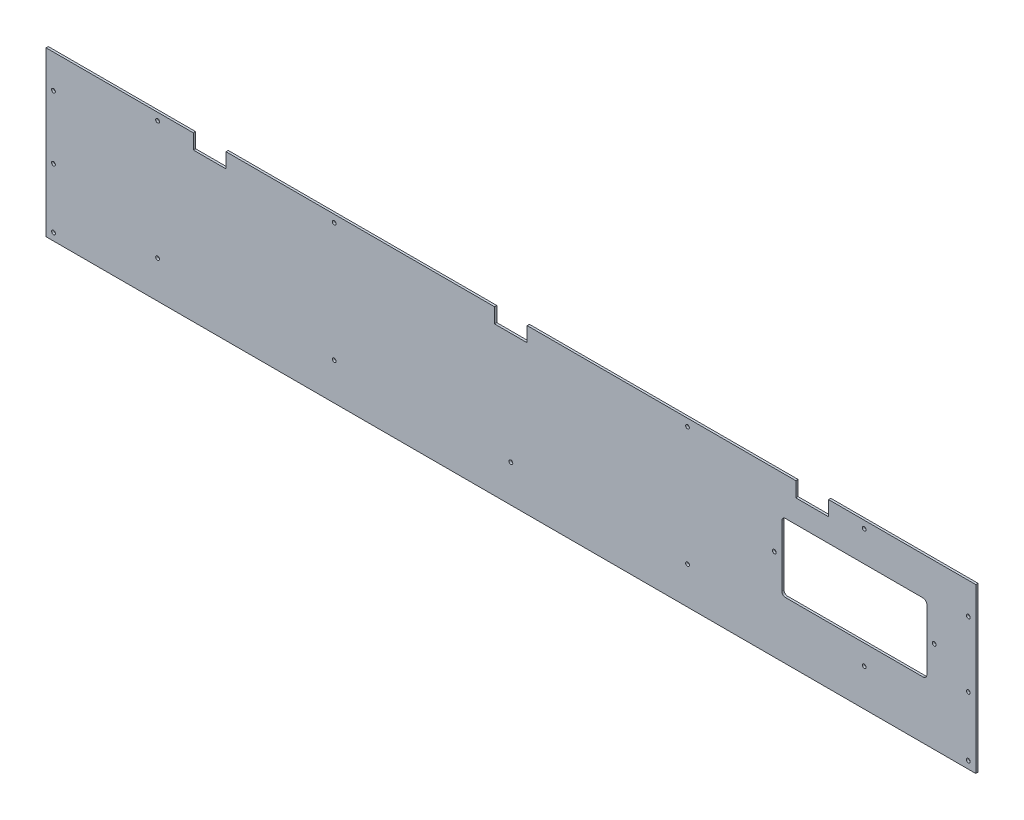
SolidWorks part; units mm, degrees
ref_plane "Front Plane" through (0, 0, 0) normal (0, 0, 1) x (1, 0, 0)
ref_plane "Top Plane" through (0, 0, 0) normal (0, 1, 0) x (1, 0, 0)
ref_plane "Right Plane" through (0, 0, 0) normal (1, 0, 0) x (0, 0, -1)
sketch "Sketch1" plane through (0, 0, 0) normal (0, 0, 1) x (1, 0, 0)
  line L0 (431.898, 87.8618) -> (629.898, 87.8618)
  line L1 (-620.102, 87.8618) -> (-422.102, 87.8618)
  line L2 (-620.102, 87.8618) -> (-620.102, -132.1382)
  line L3 (629.898, 87.8618) -> (629.898, -132.1382)
  line L7 (387.898, 67.8618) -> (431.898, 67.8618)
  line L8 (387.898, 67.8618) -> (387.898, 87.8618)
  line L9 (26.898, 87.8618) -> (387.898, 87.8618)
  line L10 (431.898, 67.8618) -> (431.898, 87.8618)
  line L11 (-17.102, 67.8618) -> (26.898, 67.8618)
  line L12 (-17.102, 67.8618) -> (-17.102, 87.8618)
  line L13 (-378.102, 87.8618) -> (-17.102, 87.8618)
  line L14 (26.898, 67.8618) -> (26.898, 87.8618)
  line L15 (4.898, -132.1382) -> (4.898, 109.214) construction
  line L16 (-422.102, 87.8618) -> (-422.102, 67.8618)
  line L17 (-422.102, 67.8618) -> (-378.102, 67.8618)
  line L18 (-378.102, 87.8618) -> (-378.102, 67.8618)
  line L20 (-620.102, -132.1382) -> (629.898, -132.1382)
  line L30 (559.1096, 36.8591) -> (374.1096, 36.8591)
  line L31 (564.1096, 31.8591) -> (564.1096, -50.1409)
  line L32 (559.1096, -55.1409) -> (374.1096, -55.1409)
  line L33 (369.1096, 31.8591) -> (369.1096, -50.1409)
  line L34 (564.1096, 36.8591) -> (369.1096, -55.1409) construction
  line L35 (564.1096, -55.1409) -> (369.1096, 36.8591) construction
  circle A0 centre (242.398, 77.8618) radius 2.55
  circle A1 centre (-610.102, 42.8618) radius 2.55
  circle A2 centre (-232.602, 77.8618) radius 2.55
  circle A3 centre (-470.102, 77.8618) radius 2.55
  circle A4 centre (479.898, 77.8618) radius 2.55
  circle A5 centre (479.898, -82.1382) radius 2.55
  circle A6 centre (242.398, -82.1382) radius 2.55
  circle A7 centre (4.898, -82.1382) radius 2.55
  circle A8 centre (-232.602, -82.1382) radius 2.55
  circle A9 centre (-470.102, -82.1382) radius 2.55
  circle A10 centre (619.898, -42.1382) radius 2.55
  circle A11 centre (-610.102, -42.1382) radius 2.55
  circle A12 centre (4.898, 77.8618) radius 2.55 [skipped]
  circle A13 centre (-610, -122.1382) radius 2.55
  circle A14 centre (619.898, 45.7053) radius 2.55
  circle A15 centre (619.898, -122.1382) radius 2.55
  circle A16 centre (574.1096, -9.1409) radius 2.55
  circle A17 centre (359.1096, -9.1409) radius 2.55
  arc A18 (369.1096, 31.8591) -> (374.1096, 36.8591) centre (374.1096, 31.8591) cw
  arc A19 (369.1096, -50.1409) -> (374.1096, -55.1409) centre (374.1096, -50.1409) ccw
  arc A20 (559.1096, -55.1409) -> (564.1096, -50.1409) centre (559.1096, -50.1409) ccw
  arc A21 (564.1096, 31.8591) -> (559.1096, 36.8591) centre (559.1096, 31.8591) ccw
  point P0 (0, 0)
  dimension "D3" = 10
  dimension "D4" = 10
  dimension "D6" = 5
  dimension "D7" = 50
  dimension "D8" = 150
  dimension "D9" = 130
  dimension "D10" = 150
  dimension "D11" = 5.1
  dimension "D18" = 220
  dimension "D22" = 10
  dimension "D23" = 5
  dimension "D17" = 45
  dimension "D25" = 10
  dimension "D14" = 10
  dimension "D21" = 10
  dimension "D28" = 10
  dimension "D29" = 130
  dimension "D35" = 92
  dimension "D36" = 195
  dimension "D2" = 1250
  dimension "D12" = 20
  dimension "D13" = 44
  dimension "D15" = 20
  dimension "D16" = 44
  dimension "D19" = 44
  dimension "D20" = 20
  dimension "D27" = 22
  dimension "D5" = 5
extrude "Boss-Extrude1" add sketch "Sketch1" along normal blind 3
